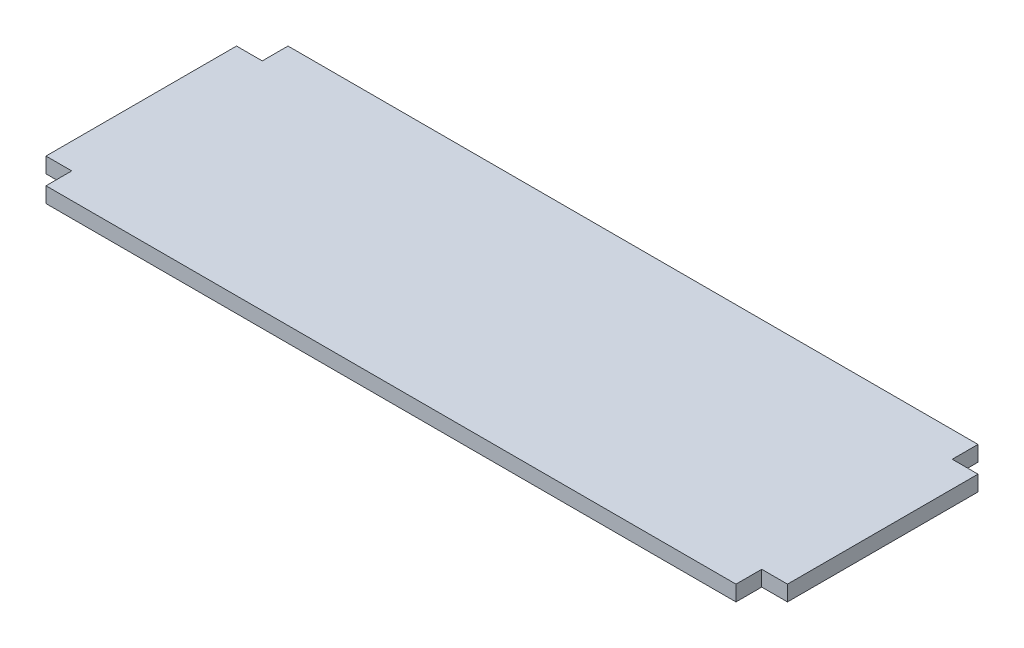
SolidWorks part; units mm, degrees
ref_plane "Front Plane" through (0, 0, 0) normal (0, 0, 1) x (1, 0, 0)
ref_plane "Top Plane" through (0, 0, 0) normal (0, 1, 0) x (1, 0, 0)
ref_plane "Right Plane" through (0, 0, 0) normal (1, 0, 0) x (0, 0, -1)
sketch "Sketch1" plane through (0, 0, 0) normal (0, 1, 0) x (1, 0, 0)
  line L16 (0, 84) -> (0, 10)
  line L19 (288, 84) -> (278, 84)
  line L20 (278, 94) -> (278, 84)
  line L23 (288, 10) -> (278, 10)
  line L24 (278, 0) -> (278, 10)
  line L27 (0, 84) -> (10, 84)
  line L28 (10, 94) -> (10, 84)
  line L31 (0, 10) -> (10, 10)
  line L32 (10, 0) -> (10, 10)
  line L33 (288, 84) -> (288, 10)
  line L34 (278, 0) -> (10, 0)
  line L35 (278, 94) -> (10, 94)
  dimension "D4" = 10
  dimension "D6" = 10
  dimension "D7" = 10
  dimension "D8" = 10
  dimension "D9" = 10
extrude "Boss-Extrude1" add sketch "Sketch1" along normal blind 6
